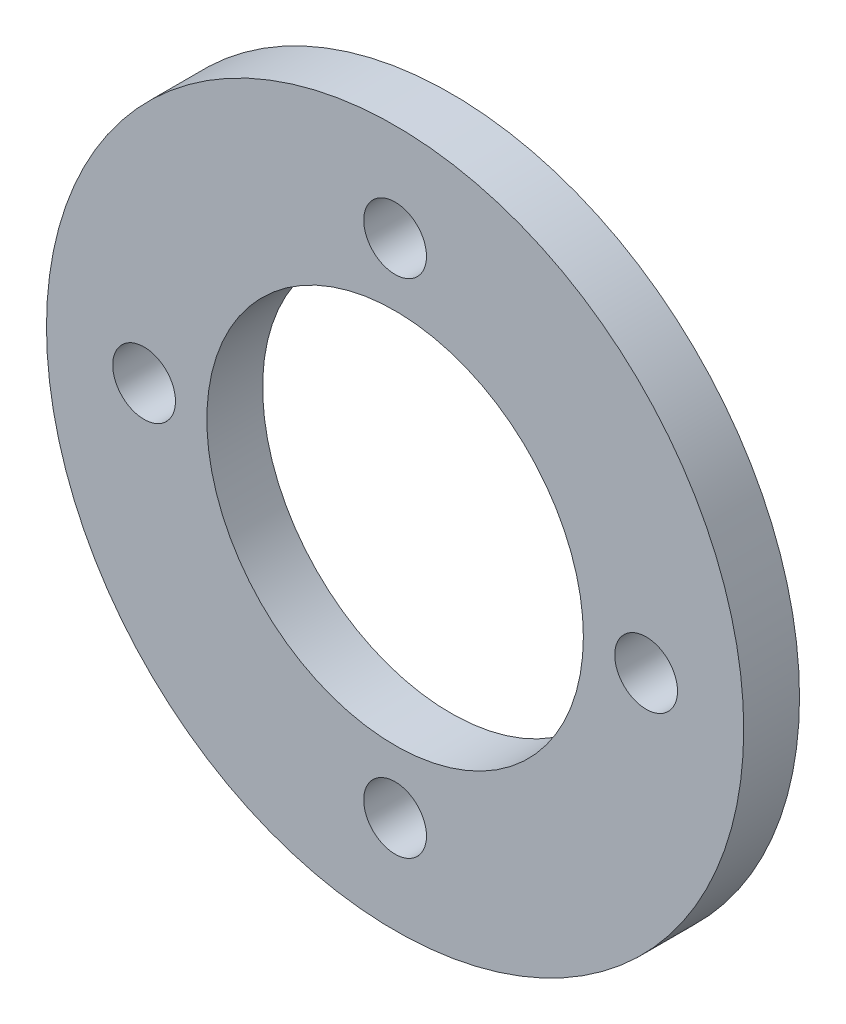
SolidWorks part; units mm, degrees
material "ABS"
ref_plane "Front Plane" through (0, 0, 0) normal (0, 0, 1) x (1, 0, 0)
ref_plane "Top Plane" through (0, 0, 0) normal (0, 1, 0) x (1, 0, 0)
ref_plane "Right Plane" through (0, 0, 0) normal (1, 0, 0) x (0, 0, -1)
sketch "Sketch1" plane through (0, 0, 0) normal (0, 0, 1) x (1, 0, 0)
  circle A0 centre (0, 0) radius 13.5
  circle A1 centre (0, 0) radius 25
  dimension "D1" = 27
  dimension "D2" = 50
extrude "Boss-Extrude1" add sketch "Sketch1" along normal blind 4
sketch "Sketch2" plane through (0, 0, 4) normal (0, 0, 1) x (1, 0, 0)
  circle A0 centre (0, 18) radius 2.25
  circle A1 centre (18, 0) radius 2.25
  circle A2 centre (0, -18) radius 2.25
  circle A3 centre (-18, 0) radius 2.25
  point P12 (0, 0)
  dimension "D1" = 4.5
  dimension "D2" = 18
  dimension "D3" = 4
extrude "Cut-Extrude1" cut sketch "Sketch2" against normal through all
